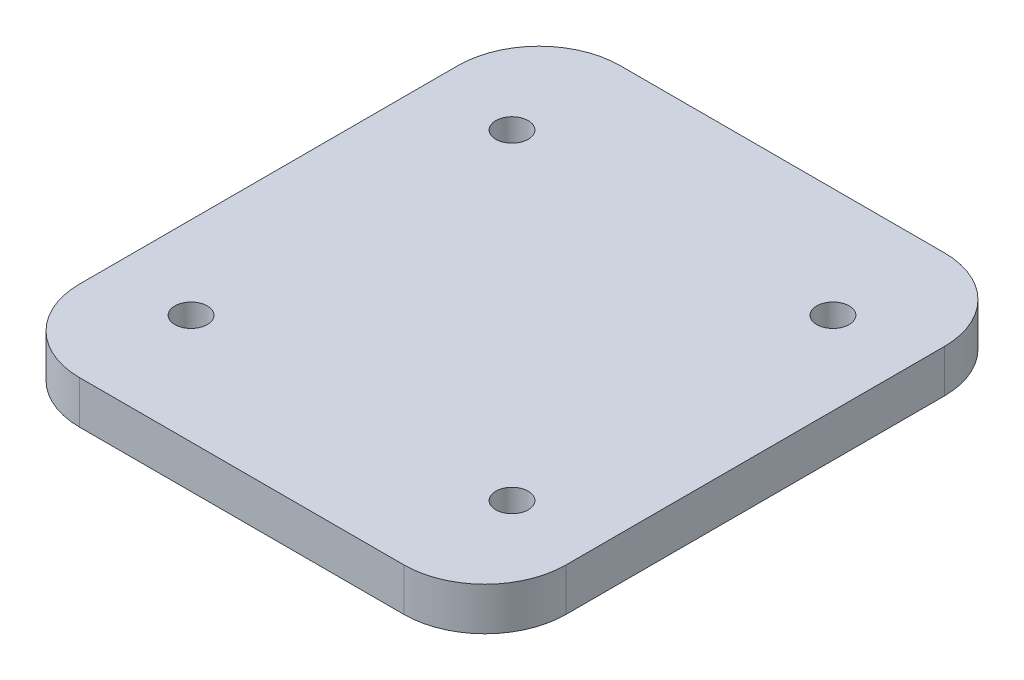
SolidWorks part; units mm, degrees
ref_plane "Front Plane" through (0, 0, 0) normal (0, 0, 1) x (1, 0, 0)
ref_plane "Top Plane" through (0, 0, 0) normal (0, 1, 0) x (1, 0, 0)
ref_plane "Right Plane" through (0, 0, 0) normal (1, 0, 0) x (0, 0, -1)
sketch "Sketch1" plane through (0, 0, 0) normal (0, 1, 0) x (1, 0, 0)
  line L1 (-24, -40) -> (24, -40)
  line L2 (-36, -28) -> (-36, 28)
  line L3 (-24, 40) -> (24, 40)
  line L4 (36, -28) -> (36, 28)
  line L5 (-36, -40) -> (36, 40) construction
  line L6 (-36, 40) -> (36, -40) construction
  arc A0 (24, 40) -> (36, 28) centre (24, 28) cw
  arc A1 (24, -40) -> (36, -28) centre (24, -28) ccw
  arc A2 (-24, -40) -> (-36, -28) centre (-24, -28) cw
  arc A3 (-36, 28) -> (-24, 40) centre (-24, 28) cw
  point P0 (0, 0)
  dimension "D1" = 12
  dimension "D2" = 80
  dimension "D3" = 72
extrude "Boss-Extrude1" add sketch "Sketch1" along normal blind 6.35
sketch "Sketch2" plane through (0, 6.35, 0) normal (0, 1, 0) x (1, 0, 0)
  line L0 (-36, 0) -> (36, 0) construction
  line L1 (-36, 28) -> (-36, -28) construction
  line L2 (36, -28) -> (36, 28) construction
  line L3 (-36, 12) -> (36, 12) construction
  line L5 (23.75, -23.75) -> (-23.75, -23.75) construction
  line L6 (23.75, -23.75) -> (23.75, 23.75) construction
  line L7 (23.75, 23.75) -> (-23.75, 23.75) construction
  line L8 (-23.75, -23.75) -> (-23.75, 23.75) construction
  line L9 (23.75, -23.75) -> (-23.75, 23.75) construction
  line L10 (23.75, 23.75) -> (-23.75, -23.75) construction
  circle A1 centre (-23.75, 23.75) radius 2.4
  circle A3 centre (23.75, 23.75) radius 2.4
  circle A4 centre (23.75, -23.75) radius 2.4
  circle A5 centre (-23.75, -23.75) radius 2.4
  point P16 (0, 0)
  dimension "D3" = 4.8
  dimension "D1" = 47.5
  dimension "D2" = 2
  dimension "D4" = 2
extrude "Cut-Extrude1" cut sketch "Sketch2" against normal through all
sketch "Sketch3" [suppressed] plane through (0, 6.35, 0) normal (0, 1, 0) x (1, 0, 0)
  line L1 (-36, 28) -> (-36, -28) construction
  line L3 (-33.5, -28) -> (-18.5, -28) construction
  line L4 (-33.5, -28) -> (-33.5, -12) construction
  line L5 (-33.5, -12) -> (-18.5, -12) construction
  line L6 (-18.5, -28) -> (-18.5, -12) construction
  line L7 (-33.5, -28) -> (-18.5, -12) construction
  line L8 (-33.5, -12) -> (-18.5, -28) construction
  circle A0 centre (-33.5, -12) radius 1.5
  circle A1 centre (-18.5, -12) radius 1.5
  circle A2 centre (-18.5, -28) radius 1.5
  circle A3 centre (-33.5, -28) radius 1.5
  point P5 (-26, -20)
  dimension "D4" = 3
  dimension "D1" = 15
  dimension "D2" = 16
  dimension "D3" = 2.5
  dimension "D5" = 20
extrude "Cut-Extrude2" [suppressed] cut sketch "Sketch3" against normal through all
